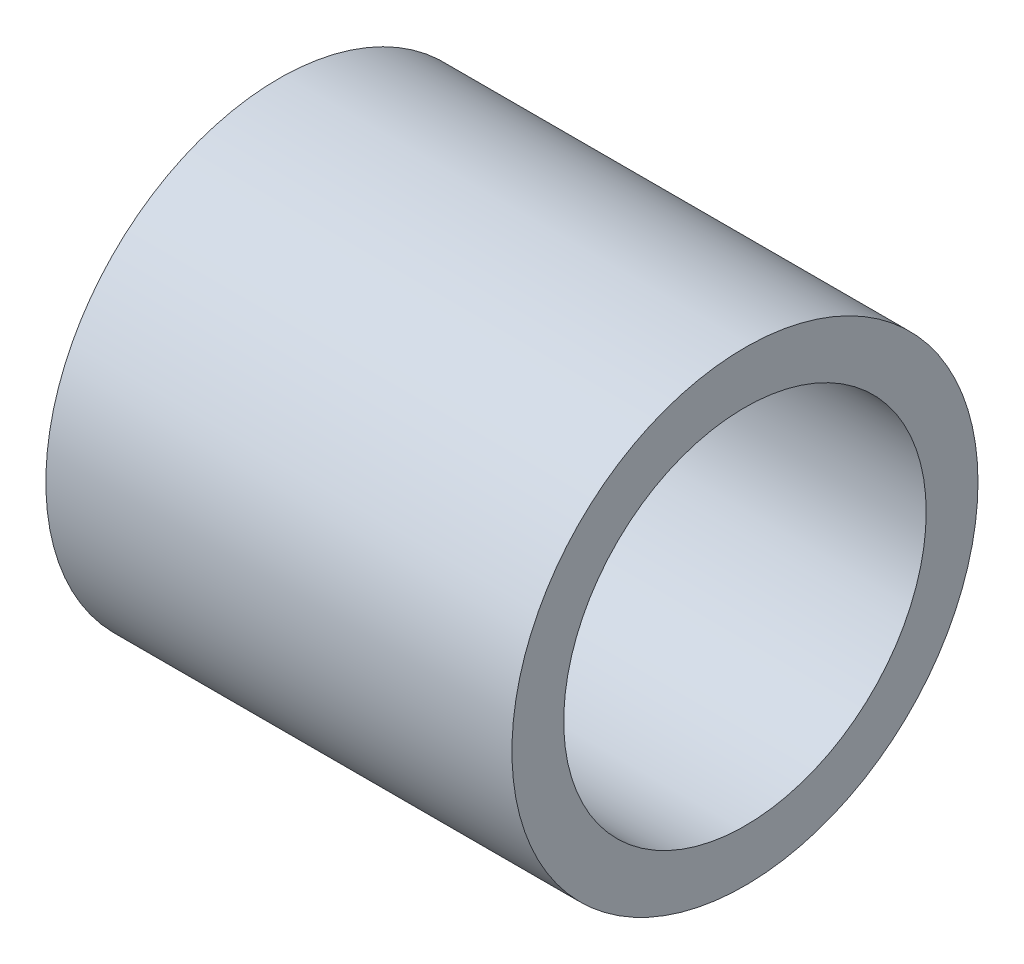
SolidWorks part; units mm, degrees
material "黄铜"
ref_plane "前视基准面" through (0, 0, 0) normal (0, 0, 1) x (1, 0, 0)
ref_plane "上视基准面" through (0, 0, 0) normal (0, 1, 0) x (1, 0, 0)
ref_plane "右视基准面" through (0, 0, 0) normal (1, 0, 0) x (0, 0, -1)
sketch "草图1" plane through (0, 0, 0) normal (1, 0, 0) x (0, 0, -1)
  circle A0 centre (0, 0) radius 7
  circle A1 centre (0, 0) radius 9
  dimension "D1" = 14
  dimension "D2" = 18
extrude "凸台-拉伸1" add sketch "草图1" against normal blind 18
